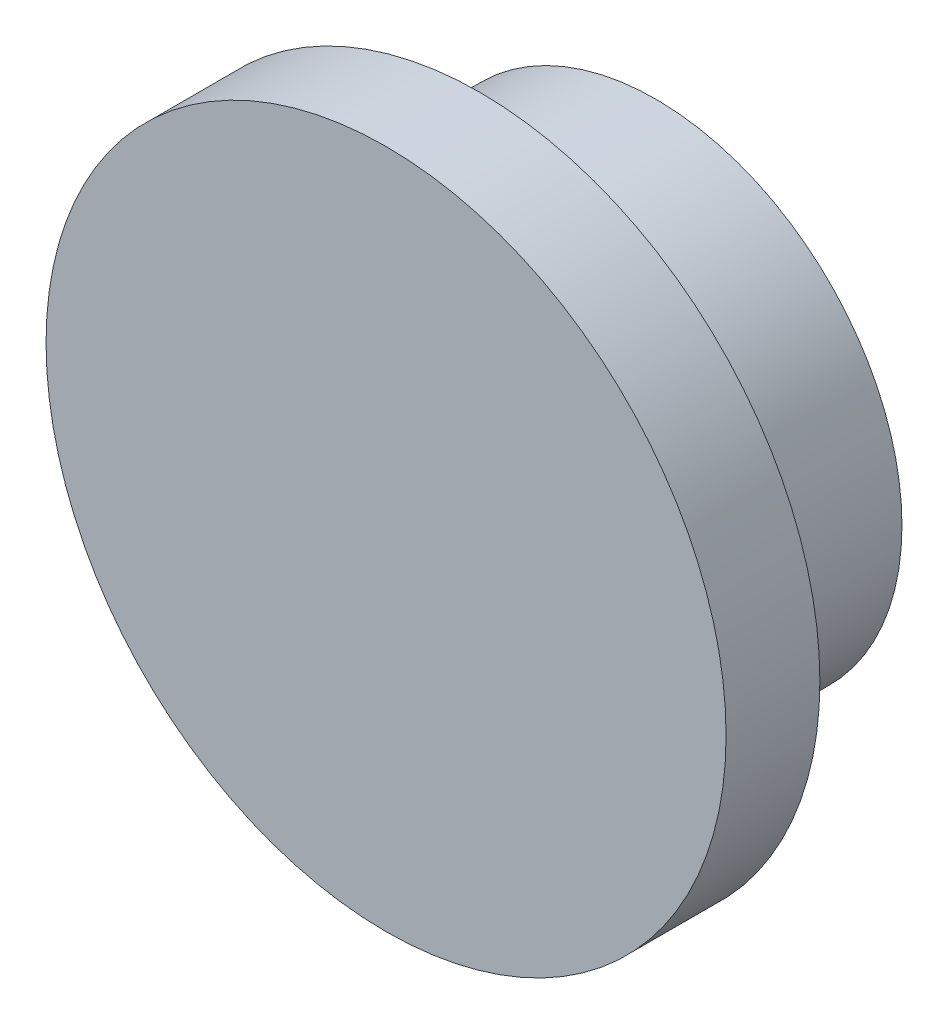
SolidWorks part; units mm, degrees
ref_plane "Front Plane" through (0, 0, 0) normal (0, 0, 1) x (1, 0, 0)
ref_plane "Top Plane" through (0, 0, 0) normal (0, 1, 0) x (1, 0, 0)
ref_plane "Right Plane" through (0, 0, 0) normal (1, 0, 0) x (0, 0, -1)
sketch "Sketch1" plane through (0, 0, 0) normal (0, 0, 1) x (1, 0, 0)
  circle A0 centre (0, 0) radius 9.2075 construction
  circle A1 centre (0, 0) radius 9.2075
extrude "Boss-Extrude1" add sketch "Sketch1" along normal blind 2.54 contours A1
sketch "Sketch2" plane through (0, 0, 0) normal (0, 0, -1) x (-1, 0, 0)
  circle A0 centre (0, 0) radius 6.6675 construction
  circle A1 centre (0, 0) radius 6.6675
  circle A2 centre (0, 0) radius 4.7625 construction
  circle A3 centre (0, 0) radius 4.7625 construction
  circle A4 centre (0, 0) radius 4.8895
  dimension "D1" = 0.127
extrude "Boss-Extrude2" add sketch "Sketch2" along normal up to surface (4.7625 mm away)
